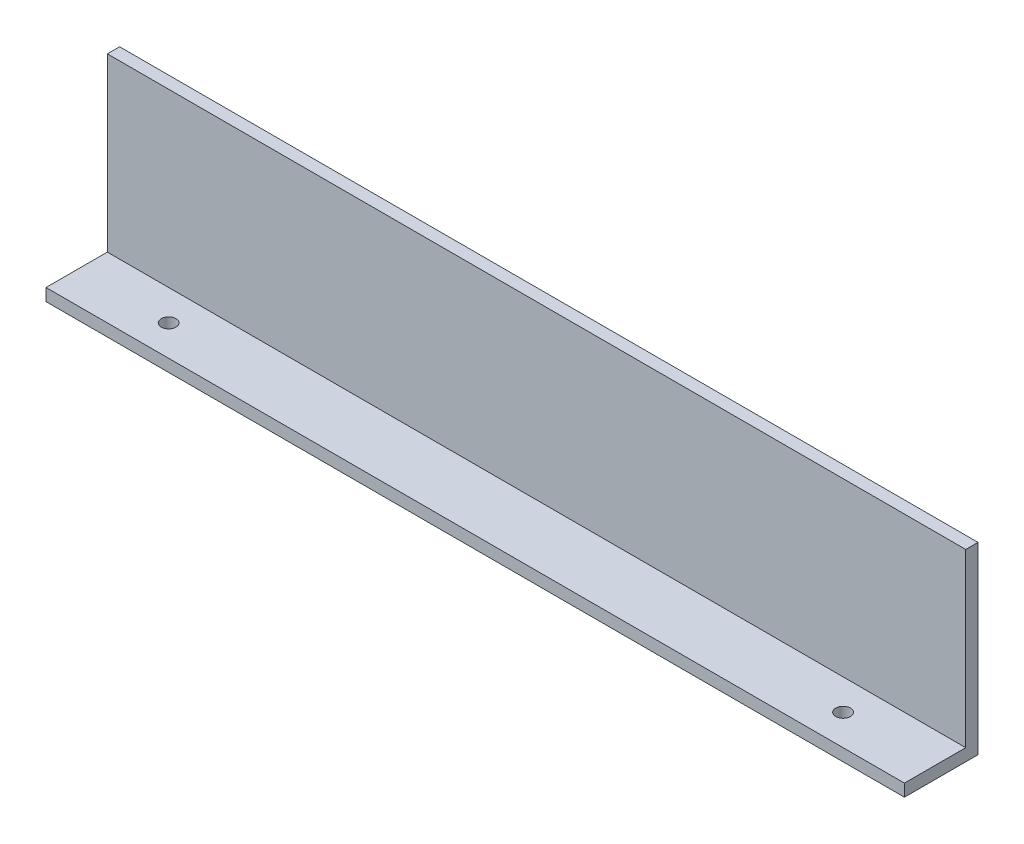
SolidWorks part; units mm, degrees
ref_plane "Płaszczyzna przednia" through (0, 0, 0) normal (0, 0, 1) x (1, 0, 0)
ref_plane "Płaszczyzna górna" through (0, 0, 0) normal (0, 1, 0) x (1, 0, 0)
ref_plane "Płaszczyzna prawa" through (0, 0, 0) normal (1, 0, 0) x (0, 0, -1)
sketch "Szkic1" plane through (0, 0, 0) normal (0, 0, 1) x (1, 0, 0)
  line L1 (-350, -75) -> (350, -75)
  line L2 (-350, -75) -> (-350, 75)
  line L3 (-350, 75) -> (350, 75)
  line L4 (350, -75) -> (350, 75)
  line L5 (-350, -75) -> (350, 75) construction
  line L6 (-350, 75) -> (350, -75) construction
  point P0 (0, 0)
  dimension "D1" = 700
  dimension "D2" = 150
extrude "Dodanie-wyciągnięcie1" add sketch "Szkic1" along normal blind 10
sketch "Szkic2" plane through (0, 0, 10) normal (0, 0, 1) x (1, 0, 0)
  line L0 (350, -75) -> (350, 75) construction
  line L1 (-350, -75) -> (350, -75)
  line L2 (-350, -75) -> (-350, -65)
  line L3 (-350, -65) -> (350, -65)
  line L4 (350, -75) -> (350, -65)
  dimension "D1" = 10
extrude "Dodanie-wyciągnięcie2" add sketch "Szkic2" along normal blind 50
hole_wizard "Otwór pod śrubę M101" positions "Szkic3" profile "Szkic4" hole size "M10" standard "Ansi Metric" end condition through all
sketch "Szkic3" plane through (0, -65, 0) normal (0, 1, 0) x (1, 0, 0)
  line L0 (350, -60) -> (-350, -60) construction
  line L1 (-350, -60) -> (-350, -10) construction
  point P0 (-275, -35)
  dimension "D1" = 25
  dimension "D2" = 75
sketch "Szkic4" plane through (-275, -65, 35) normal (1, 0, 0) x (0, 0, 1)
  line L0 (0, 0) -> (0, 10)
  line L1 (0, 10) -> (6, 10)
  line L2 (6, 10) -> (6, 0)
  line L5 (6, 0) -> (0, 0)
  line L11 (0, -6.35) -> (0, 107.95) construction
  dimension "Średnica otworu na wylot" = 12
  dimension "Głębokość otworu na wylot" = 10
pattern_linear "Szyk liniowy2" count 2 spacing 550 along (1, 0, 0) of "Otwór pod śrubę M101"
